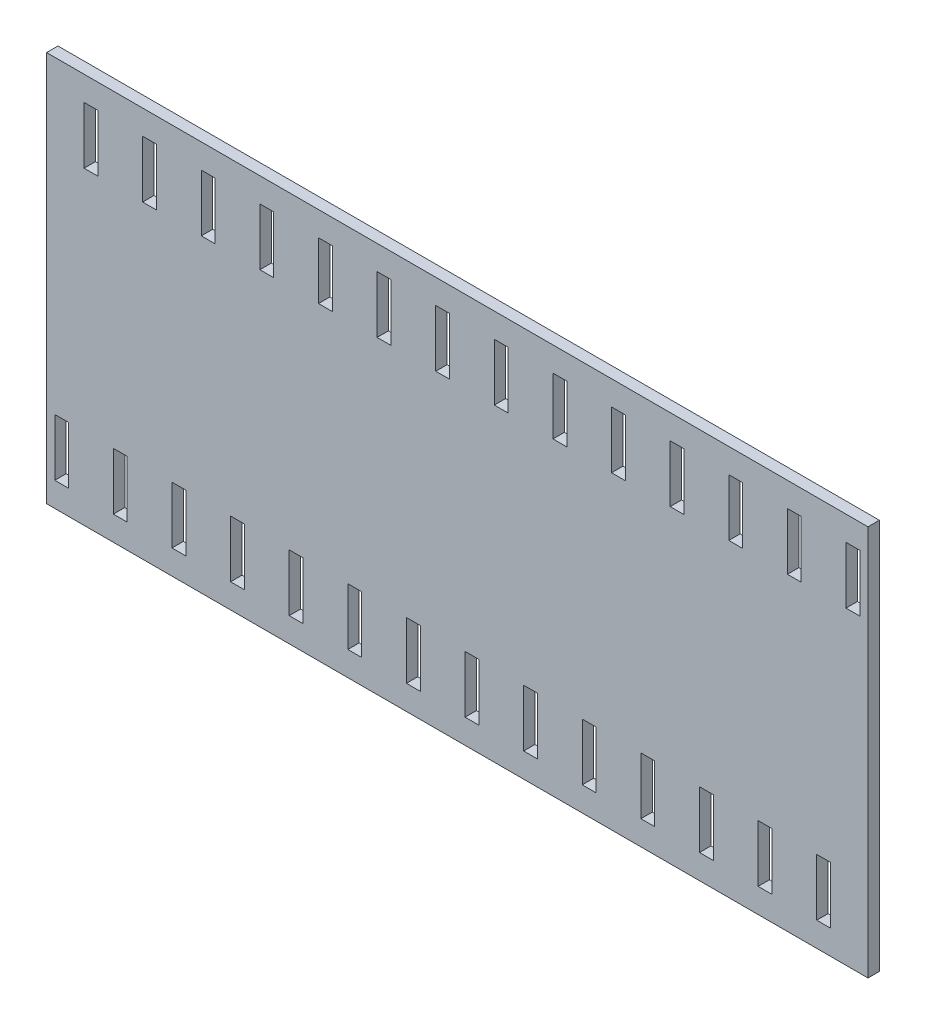
SolidWorks part; units mm, degrees
ref_plane "Plan de face" through (0, 0, 0) normal (0, 0, 1) x (1, 0, 0)
ref_plane "Plan de dessus" through (0, 0, 0) normal (0, 1, 0) x (1, 0, 0)
ref_plane "Plan de droite" through (0, 0, 0) normal (1, 0, 0) x (0, 0, -1)
sketch "Esquisse1" plane through (0, 0, 0) normal (0, 0, 1) x (1, 0, 0)
  line L1 (-50.45, -24) -> (50.45, -24)
  line L2 (-50.45, -24) -> (-50.45, 24)
  line L3 (-50.45, 24) -> (50.45, 24)
  line L4 (50.45, -24) -> (50.45, 24)
  line L5 (-50.45, -24) -> (50.45, 24) construction
  line L6 (-50.45, 24) -> (50.45, -24) construction
  point P0 (0, 0)
  dimension "D1" = 100.9
  dimension "D2" = 48
extrude "Boss.-Extru.1" add sketch "Esquisse1" along normal blind 1.4
sketch "Esquisse2" plane through (0, 0, 0) normal (0, 0, -1) x (-1, 0, 0)
  line L0 (-50.45, -24) -> (-50.45, 24) construction
  line L1 (-49.45, 21) -> (-47.75, 21)
  line L2 (-49.45, 21) -> (-49.45, 14)
  line L3 (-49.45, 14) -> (-47.75, 14)
  line L4 (-47.75, 21) -> (-47.75, 14)
  line L5 (-50.45, 24) -> (50.45, 24) construction
  line L6 (-42.25, 21) -> (-42.25, 14)
  line L7 (-42.25, 21) -> (-40.55, 21)
  line L8 (-40.55, 21) -> (-40.55, 14)
  line L9 (-42.25, 14) -> (-40.55, 14)
  line L10 (-35.05, 21) -> (-35.05, 14)
  line L11 (-35.05, 21) -> (-33.35, 21)
  line L12 (-33.35, 21) -> (-33.35, 14)
  line L13 (-35.05, 14) -> (-33.35, 14)
  line L14 (-27.85, 21) -> (-27.85, 14)
  line L15 (-27.85, 21) -> (-26.15, 21)
  line L16 (-26.15, 21) -> (-26.15, 14)
  line L17 (-27.85, 14) -> (-26.15, 14)
  line L18 (-20.65, 21) -> (-20.65, 14)
  line L19 (-20.65, 21) -> (-18.95, 21)
  line L20 (-18.95, 21) -> (-18.95, 14)
  line L21 (-20.65, 14) -> (-18.95, 14)
  line L22 (-13.45, 21) -> (-13.45, 14)
  line L23 (-13.45, 21) -> (-11.75, 21)
  line L24 (-11.75, 21) -> (-11.75, 14)
  line L25 (-13.45, 14) -> (-11.75, 14)
  line L26 (-6.25, 21) -> (-6.25, 14)
  line L27 (-6.25, 21) -> (-4.55, 21)
  line L28 (-4.55, 21) -> (-4.55, 14)
  line L29 (-6.25, 14) -> (-4.55, 14)
  line L30 (0.95, 21) -> (0.95, 14)
  line L31 (0.95, 21) -> (2.65, 21)
  line L32 (2.65, 21) -> (2.65, 14)
  line L33 (0.95, 14) -> (2.65, 14)
  line L34 (8.15, 21) -> (8.15, 14)
  line L35 (8.15, 21) -> (9.85, 21)
  line L36 (9.85, 21) -> (9.85, 14)
  line L37 (8.15, 14) -> (9.85, 14)
  line L38 (15.35, 21) -> (15.35, 14)
  line L39 (15.35, 21) -> (17.05, 21)
  line L40 (17.05, 21) -> (17.05, 14)
  line L41 (15.35, 14) -> (17.05, 14)
  line L42 (22.55, 21) -> (22.55, 14)
  line L43 (22.55, 21) -> (24.25, 21)
  line L44 (24.25, 21) -> (24.25, 14)
  line L45 (22.55, 14) -> (24.25, 14)
  line L46 (29.75, 21) -> (29.75, 14)
  line L47 (29.75, 21) -> (31.45, 21)
  line L48 (31.45, 21) -> (31.45, 14)
  line L49 (29.75, 14) -> (31.45, 14)
  line L50 (36.95, 21) -> (36.95, 14)
  line L51 (36.95, 21) -> (38.65, 21)
  line L52 (38.65, 21) -> (38.65, 14)
  line L53 (36.95, 14) -> (38.65, 14)
  line L54 (44.15, 21) -> (44.15, 14)
  line L55 (44.15, 21) -> (45.85, 21)
  line L56 (45.85, 21) -> (45.85, 14)
  line L57 (44.15, 14) -> (45.85, 14)
  line L58 (50.45, -24) -> (-50.45, -24) construction
  line L59 (-45.85, -14) -> (-44.15, -14)
  line L60 (-45.85, -14) -> (-45.85, -21)
  line L61 (-45.85, -21) -> (-44.15, -21)
  line L62 (-44.15, -14) -> (-44.15, -21)
  line L63 (-38.65, -14) -> (-38.65, -21)
  line L64 (-38.65, -14) -> (-36.95, -14)
  line L65 (-36.95, -14) -> (-36.95, -21)
  line L66 (-38.65, -21) -> (-36.95, -21)
  line L67 (-31.45, -14) -> (-31.45, -21)
  line L68 (-31.45, -14) -> (-29.75, -14)
  line L69 (-29.75, -14) -> (-29.75, -21)
  line L70 (-31.45, -21) -> (-29.75, -21)
  line L71 (-24.25, -14) -> (-24.25, -21)
  line L72 (-24.25, -14) -> (-22.55, -14)
  line L73 (-22.55, -14) -> (-22.55, -21)
  line L74 (-24.25, -21) -> (-22.55, -21)
  line L75 (-17.05, -14) -> (-17.05, -21)
  line L76 (-17.05, -14) -> (-15.35, -14)
  line L77 (-15.35, -14) -> (-15.35, -21)
  line L78 (-17.05, -21) -> (-15.35, -21)
  line L79 (-9.85, -14) -> (-9.85, -21)
  line L80 (-9.85, -14) -> (-8.15, -14)
  line L81 (-8.15, -14) -> (-8.15, -21)
  line L82 (-9.85, -21) -> (-8.15, -21)
  line L83 (-2.65, -14) -> (-2.65, -21)
  line L84 (-2.65, -14) -> (-0.95, -14)
  line L85 (-0.95, -14) -> (-0.95, -21)
  line L86 (-2.65, -21) -> (-0.95, -21)
  line L87 (4.55, -14) -> (4.55, -21)
  line L88 (4.55, -14) -> (6.25, -14)
  line L89 (6.25, -14) -> (6.25, -21)
  line L90 (4.55, -21) -> (6.25, -21)
  line L91 (11.75, -14) -> (11.75, -21)
  line L92 (11.75, -14) -> (13.45, -14)
  line L93 (13.45, -14) -> (13.45, -21)
  line L94 (11.75, -21) -> (13.45, -21)
  line L95 (18.95, -14) -> (18.95, -21)
  line L96 (18.95, -14) -> (20.65, -14)
  line L97 (20.65, -14) -> (20.65, -21)
  line L98 (18.95, -21) -> (20.65, -21)
  line L99 (26.15, -14) -> (26.15, -21)
  line L100 (26.15, -14) -> (27.85, -14)
  line L101 (27.85, -14) -> (27.85, -21)
  line L102 (26.15, -21) -> (27.85, -21)
  line L103 (33.35, -14) -> (33.35, -21)
  line L104 (33.35, -14) -> (35.05, -14)
  line L105 (35.05, -14) -> (35.05, -21)
  line L106 (33.35, -21) -> (35.05, -21)
  line L107 (40.55, -14) -> (40.55, -21)
  line L108 (40.55, -14) -> (42.25, -14)
  line L109 (42.25, -14) -> (42.25, -21)
  line L110 (40.55, -21) -> (42.25, -21)
  line L111 (47.75, -14) -> (47.75, -21)
  line L112 (47.75, -14) -> (49.45, -14)
  line L113 (49.45, -14) -> (49.45, -21)
  line L114 (47.75, -21) -> (49.45, -21)
  dimension "D1" = 1
  dimension "D2" = 1.7
  dimension "D3" = 7
  dimension "D4" = 3
  dimension "D6" = 1.7
  dimension "D7" = 7
  dimension "D8" = 3
  dimension "D9" = 4.6
  dimension "D5" = 14
  dimension "D10" = 14
extrude "Enlèv. mat.-Extru.1" cut sketch "Esquisse2" against normal through all
sketch "Esquisse3" plane through (0, 0, 0) normal (0, 0, -1) x (-1, 0, 0)
  text T0 "KR   DESOLVATION"
extrude "Enlèv. mat.-Extru.2" cut sketch "Esquisse3" against normal blind 0.1
